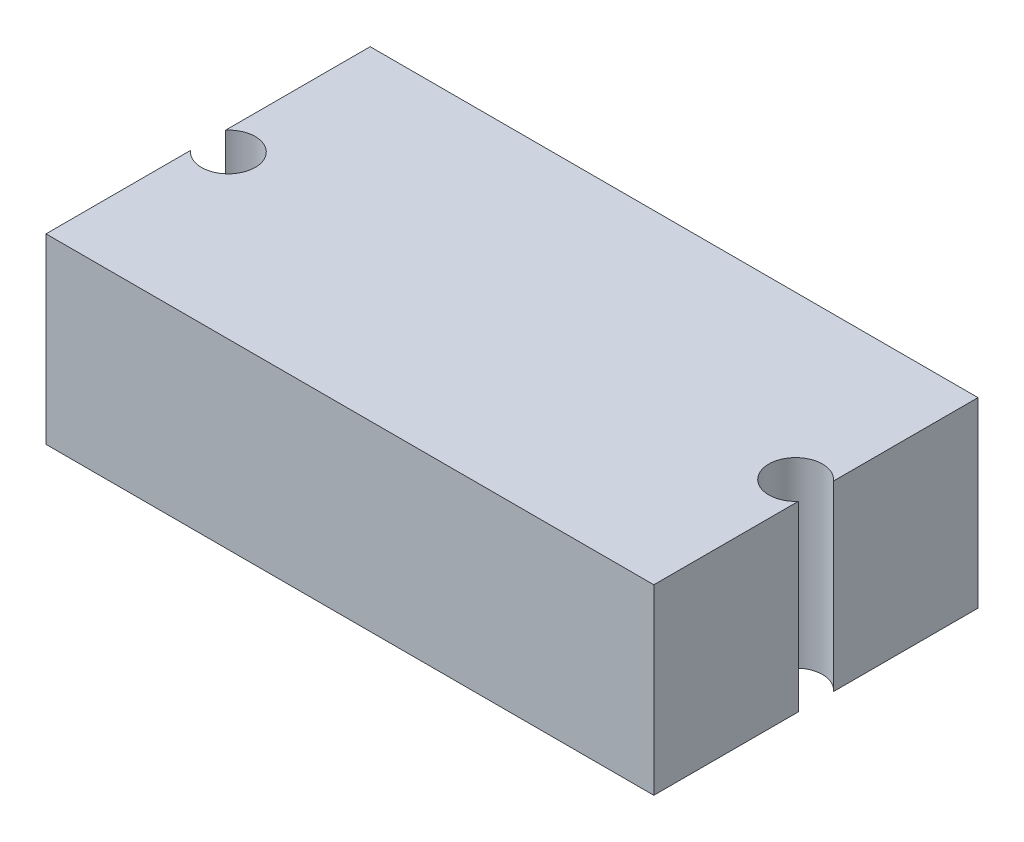
SolidWorks part; units mm, degrees
ref_plane "前视基准面" through (0, 0, 0) normal (0, 0, 1) x (1, 0, 0)
ref_plane "上视基准面" through (0, 0, 0) normal (0, 1, 0) x (1, 0, 0)
ref_plane "右视基准面" through (0, 0, 0) normal (1, 0, 0) x (0, 0, -1)
sketch "草图1" plane through (0, 0, 0) normal (0, 1, 0) x (1, 0, 0)
  line L1 (-30, 16) -> (30, 16)
  line L2 (-30, 16) -> (-30, -16)
  line L3 (-30, -16) -> (30, -16)
  line L4 (30, 16) -> (30, -16)
  line L5 (-30, 16) -> (30, -16) construction
  line L6 (-30, -16) -> (30, 16) construction
  point P0 (0, 0)
  dimension "D1" = 60
  dimension "D2" = 32
extrude "凸台-拉伸1" add sketch "草图1" along normal blind 18
sketch "草图2" plane through (0, 18, 0) normal (0, 1, 0) x (1, 0, 0)
  line L0 (-28, 0) -> (28, 0) construction
  circle A0 centre (-28, 0) radius 2.65
  circle A1 centre (28, 0) radius 2.65
  point P4 (0, 0)
  dimension "D1" = 5.3
  dimension "D2" = 56
extrude "切除-拉伸1" cut sketch "草图2" against normal through all
